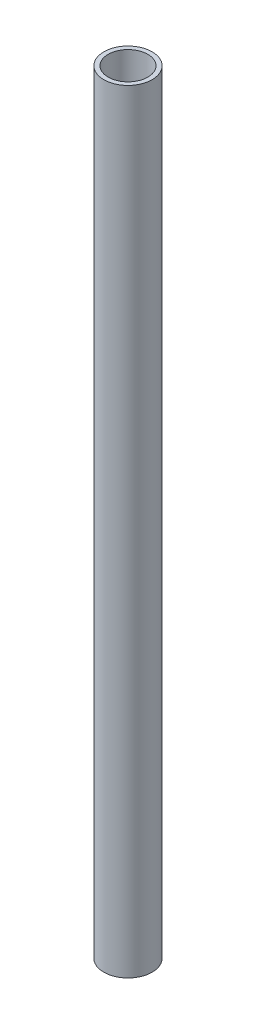
SolidWorks part; units mm, degrees
ref_plane "Front Plane" through (0, 0, 0) normal (0, 0, 1) x (1, 0, 0)
ref_plane "Top Plane" through (0, 0, 0) normal (0, 1, 0) x (1, 0, 0)
ref_plane "Right Plane" through (0, 0, 0) normal (1, 0, 0) x (0, 0, -1)
sketch "Sketch1" plane through (0, 0, 0) normal (0, 1, 0) x (1, 0, 0)
  circle A0 centre (0, 0) radius 12.7
  circle A1 centre (0, 0) radius 10.414
  dimension "D1" = 25.4
  dimension "D2" = 20.828
extrude "Boss-Extrude1" add sketch "Sketch1" along normal blind 406.4
